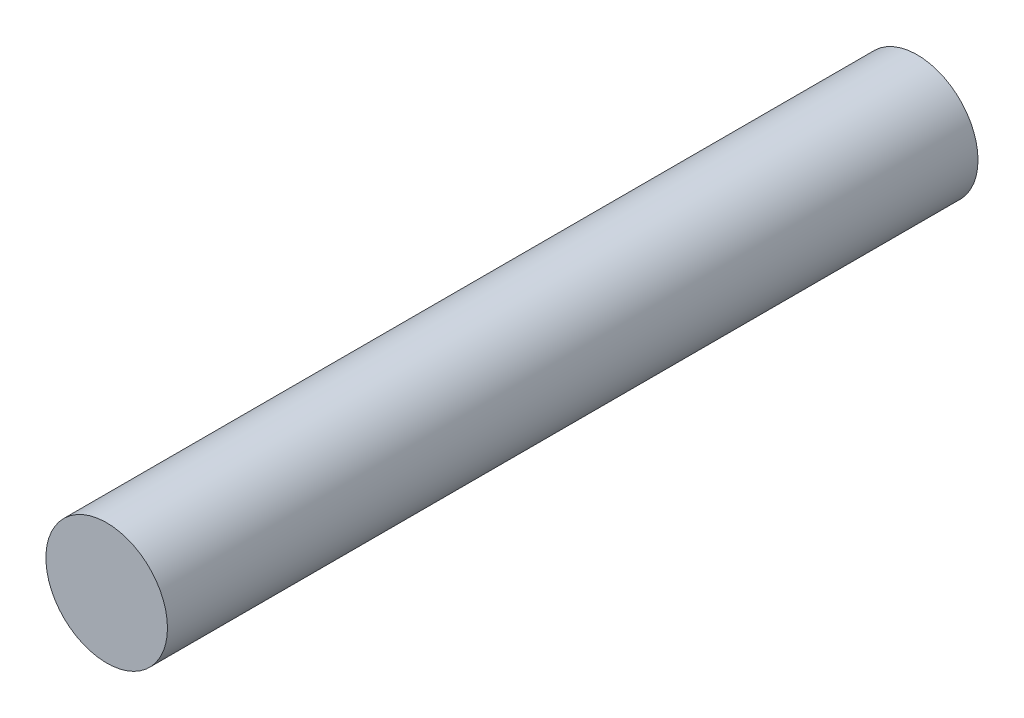
SolidWorks part; units mm, degrees
ref_plane "Plan de face" through (0, 0, 0) normal (0, 0, 1) x (1, 0, 0)
ref_plane "Plan de dessus" through (0, 0, 0) normal (0, 1, 0) x (1, 0, 0)
ref_plane "Plan de droite" through (0, 0, 0) normal (1, 0, 0) x (0, 0, -1)
sketch "Esquisse1" plane through (0, 0, 0) normal (0, 1, 0) x (1, 0, 0)
  line L0 (1.5, 0) -> (0, 0)
  line L1 (0, 0) -> (0, -20)
  line L2 (0, -20) -> (1.5, -20)
  line L3 (1.5, -20) -> (1.5, 0)
  line L4 (0, 0) -> (0, -20) construction
revolve "Révolution1" add sketch "Esquisse1" angle 360 about L4
